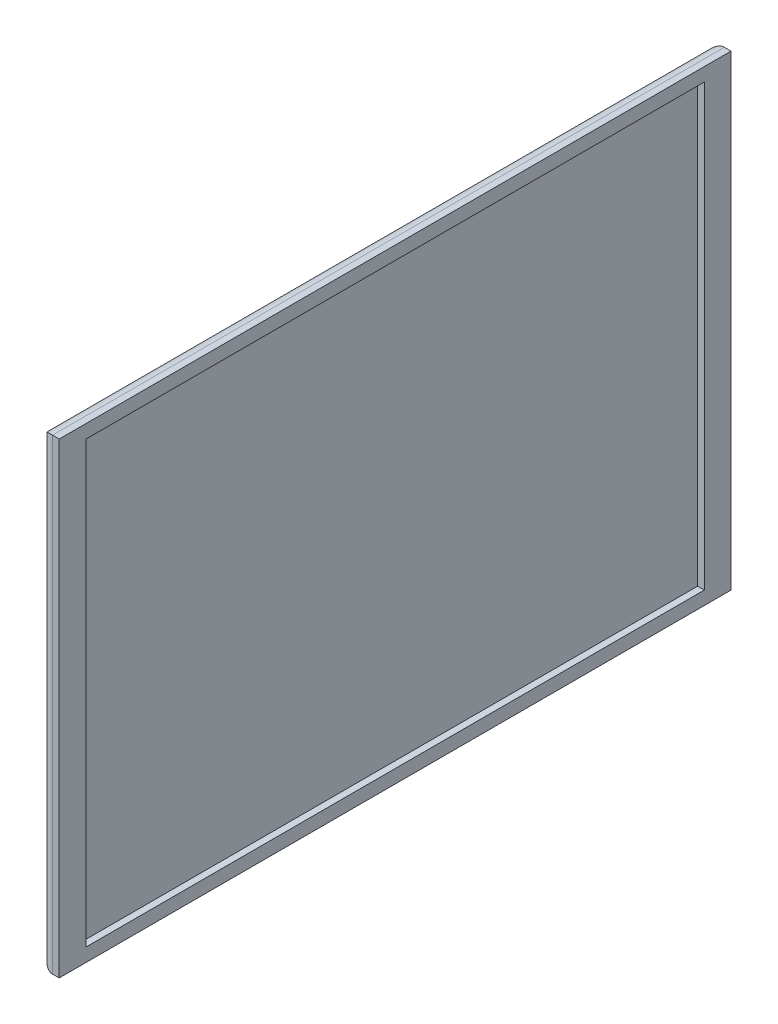
SolidWorks part; units mm, degrees
ref_plane "Front Plane" through (0, 0, 0) normal (0, 0, 1) x (1, 0, 0)
ref_plane "Top Plane" through (0, 0, 0) normal (0, 1, 0) x (1, 0, 0)
ref_plane "Right Plane" through (0, 0, 0) normal (1, 0, 0) x (0, 0, -1)
sketch "Sketch1" plane through (0, 0, 0) normal (1, 0, 0) x (0, 0, -1)
  line L0 (0, -12.2843) -> (0, 12.2843) construction
  line L1 (-17.4448, 0) -> (17.4448, 0) construction
  line L3 (-12.53, 8.705) -> (12.53, 8.705)
  line L4 (-12.53, 8.705) -> (-12.53, -8.705)
  line L5 (-12.53, -8.705) -> (12.53, -8.705)
  line L6 (12.53, 8.705) -> (12.53, -8.705)
  line L7 (-12.53, 8.705) -> (12.53, -8.705) construction
  line L8 (-12.53, -8.705) -> (12.53, 8.705) construction
  point P0 (0, 0)
  point P4 (0, 0)
  point P8 (0, 0)
  dimension "D1" = 17.41
  dimension "D2" = 25.06
extrude "Boss-Extrude1" add sketch "Sketch1" along normal blind 0.75
fillet "Fillet4" radius 0.5 4 edges at (0, -8.705, 0) (0, 0, -12.53) (0, 0, 12.53) (0, 8.705, 0)
sketch "Sketch2" plane through (0.75, 0, 0) normal (1, 0, 0) x (0, 0, -1)
  line L0 (12.53, 8.705) -> (-12.53, 8.705) construction
  line L1 (-11.53, 8.205) -> (11.53, 8.205)
  line L2 (-11.53, 8.205) -> (-11.53, -8.205)
  line L3 (-11.53, -8.205) -> (11.53, -8.205)
  line L4 (11.53, 8.205) -> (11.53, -8.205)
  line L5 (-11.53, 8.205) -> (11.53, -8.205) construction
  line L6 (-11.53, -8.205) -> (11.53, 8.205) construction
  line L7 (12.53, -8.705) -> (12.53, 8.705) construction
  point P0 (0, 0)
  dimension "D1" = 0.5
  dimension "D2" = 1
extrude "Cut-Extrude1" cut sketch "Sketch2" against normal blind 0.25 contours L2 L1 L4 L3
scale "Scale1" bodies to scale 102 scale about centroid uniform scaling yes scale factor 10
